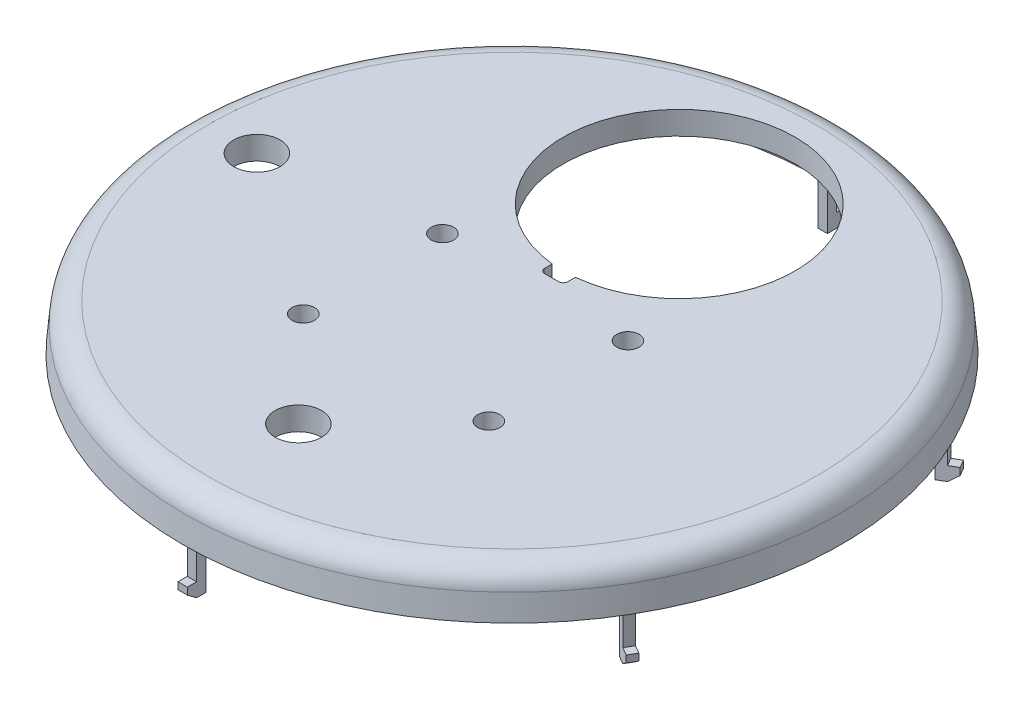
SolidWorks part; units mm, degrees
ref_plane "Front Plane" through (0, 0, 0) normal (0, 0, 1) x (1, 0, 0)
ref_plane "Top Plane" through (0, 0, 0) normal (0, 1, 0) x (1, 0, 0)
ref_plane "Right Plane" through (0, 0, 0) normal (1, 0, 0) x (0, 0, -1)
sketch "Sketch1" plane through (0, 0, 0) normal (0, 1, 0) x (1, 0, 0)
  circle A0 centre (0, 0) radius 71.05
  dimension "D1" = 142.1
extrude "Boss-Extrude1" add sketch "Sketch1" along normal blind 10 draft 5
shell "Shell4" thickness 5
sketch "Sketch2" plane through (0, 10, 0) normal (0, 1, 0) x (1, 0, 0)
  circle A0 centre (0, -46.05) radius 5
  circle A1 centre (0, 36.05) radius 25
  circle A2 centre (20, 5) radius 2.413
  circle A3 centre (20, -25) radius 2.413
  circle A4 centre (-20, -25) radius 2.413
  circle A5 centre (-20, 5) radius 2.413
  dimension "D1" = 10
  dimension "D3" = 50
  dimension "D5" = 4.826
  dimension "D6" = 4.826
  dimension "D7" = 4.826
  dimension "D8" = 4.826
  dimension "D2" = 46.05
  dimension "D4" = 36.05
  dimension "D9" = 5
  dimension "D10" = 25
  dimension "D11" = 20
  dimension "D12" = 20
  dimension "D13" = 5
extrude "Cut-Extrude1" cut sketch "Sketch2" against normal through all
sketch "Sketch3" plane through (0, 10, 0) normal (0, 1, 0) x (1, 0, 0)
  line L0 (0, 0) -> (0, 17.3356) construction
  line L1 (0, 17.3356) -> (0, 0) construction
  line L2 (0, 0) -> (-9.5982, 0) construction
  circle A0 centre (37.5, 42) radius 2.413
  circle A1 centre (-37.5, 42) radius 2.413
  circle A2 centre (37.5, -42) radius 2.413
  circle A3 centre (-37.5, -42) radius 2.413
  dimension "D3" = 4.826
  dimension "D1" = 37.5
  dimension "D2" = 42
extrude "Cut-Extrude2" [suppressed] cut sketch "Sketch3" against normal through all and the other way through all
sketch "Sketch4" [suppressed] plane through (0, 5, 0) normal (0, -1, 0) x (-1, 0, 0)
  circle A0 centre (37.5, -42) radius 4.826
  circle A1 centre (-37.5, -42) radius 4.826
  circle A2 centre (-37.5, 42) radius 4.826
  circle A3 centre (37.5, 42) radius 4.826
  dimension "D1" = 9.652
  dimension "D2" = 9.652
  dimension "D3" = 9.652
  dimension "D4" = 9.652
extrude "Boss-Extrude2" [suppressed] add sketch "Sketch4" along normal blind 5
sketch "Sketch5" [suppressed] plane through (0, 0, 0) normal (0, -1, 0) x (-1, 0, 0)
  circle A0 centre (37.5, -42) radius 2.413
  circle A1 centre (-37.5, -42) radius 2.413
  circle A2 centre (-37.5, 42) radius 2.413
  circle A3 centre (37.5, 42) radius 2.413
  dimension "D1" = 4.826
  dimension "D2" = 4.826
  dimension "D3" = 4.826
  dimension "D4" = 4.826
extrude "Cut-Extrude3" [suppressed] cut sketch "Sketch5" against normal through all
sketch "Sketch6" plane through (0, 10, 0) normal (0, 1, 0) x (1, 0, 0)
  line L0 (-25, 36.05) -> (25, 36.05) construction
  line L1 (-2.5, 14.1871) -> (2.5, 14.1871)
  line L2 (-2.5, 14.1871) -> (-2.5, 9.55)
  line L3 (-1.5, 8.55) -> (1.5, 8.55)
  line L4 (2.5, 14.1871) -> (2.5, 9.55)
  line L5 (0, 36.05) -> (0, 43.4762) construction
  circle A0 centre (0, 36.05) radius 25 construction
  arc A1 (1.5, 8.55) -> (2.5, 9.55) centre (1.5, 9.55) ccw
  arc A2 (-2.5, 9.55) -> (-1.5, 8.55) centre (-1.5, 9.55) ccw
  point P16 (0, 39.7631)
  dimension "D3" = 1
  dimension "D1" = 27.5
  dimension "D2" = 5
  dimension "D4" = 2.5
extrude "Cut-Extrude4" cut sketch "Sketch6" against normal blind 10
sketch "Sketch7" plane through (0, 10, 0) normal (0, 1, 0) x (1, 0, 0)
  line L0 (0, 36.05) -> (0, 46.1727) construction
  line L1 (0, 46.1727) -> (-8.9236, 36.05) construction
  line L2 (-8.9236, 36.05) -> (0, 36.05) construction
  circle A0 centre (-33, 30.05) radius 2.413
  circle A1 centre (33, 30.05) radius 2.413
  dimension "D1" = 4.826
  dimension "D2" = 4.826
  dimension "D3" = 6
  dimension "D4" = 6
  dimension "D5" = 33
  dimension "D6" = 33
extrude "Cut-Extrude5" [suppressed] cut sketch "Sketch7" against normal through all
fillet "Fillet1" [suppressed] radius 1
fillet "Fillet2" radius 5 1 edges at (0, 10, 70.1751)
sketch "Sketch8" [suppressed] plane through (0, 5, 0) normal (0, -1, 0) x (-1, 0, 0)
  line L0 (-37.5, -42) -> (-45.6959, -42) construction
  line L1 (-33.7739, -43.25) -> (-25.174, -43.25)
  line L2 (-33.7739, -43.25) -> (-33.7739, -40.75)
  line L3 (-33.7739, -40.75) -> (-25.174, -40.75)
  line L4 (-25.174, -43.25) -> (-25.174, -40.75)
  line L5 (-36.25, -38.3837) -> (-38.75, -38.3837)
  line L6 (-36.25, -38.3837) -> (-36.25, -29.674)
  line L7 (-36.25, -29.674) -> (-38.75, -29.674)
  line L8 (-38.75, -38.3837) -> (-38.75, -29.674)
  line L9 (-45.6959, -42) -> (-37.5, -45.4738) construction
  line L10 (-37.5, -45.4738) -> (-37.5, -42) construction
  line L11 (0, 0) -> (0, -9.0235) construction
  line L12 (36.25, -29.674) -> (38.75, -29.674)
  line L13 (38.75, -38.3837) -> (38.75, -29.674)
  line L14 (36.25, -38.3837) -> (38.75, -38.3837)
  line L15 (36.25, -38.3837) -> (36.25, -29.674)
  line L16 (33.7739, -40.75) -> (25.174, -40.75)
  line L17 (25.174, -43.25) -> (25.174, -40.75)
  line L18 (33.7739, -43.25) -> (25.174, -43.25)
  line L19 (33.7739, -43.25) -> (33.7739, -40.75)
  line L20 (0, 0) -> (-8.6355, 0) construction
  line L21 (-36.25, 29.674) -> (-38.75, 29.674)
  line L22 (-38.75, 38.3837) -> (-38.75, 29.674)
  line L23 (-36.25, 38.3837) -> (-38.75, 38.3837)
  line L24 (-36.25, 38.3837) -> (-36.25, 29.674)
  line L25 (-33.7739, 40.75) -> (-25.174, 40.75)
  line L26 (-25.174, 43.25) -> (-25.174, 40.75)
  line L27 (-33.7739, 43.25) -> (-25.174, 43.25)
  line L28 (-33.7739, 43.25) -> (-33.7739, 40.75)
  line L29 (36.25, 38.3837) -> (36.25, 29.674)
  line L30 (36.25, 38.3837) -> (38.75, 38.3837)
  line L31 (38.75, 38.3837) -> (38.75, 29.674)
  line L32 (36.25, 29.674) -> (38.75, 29.674)
  line L33 (33.7739, 43.25) -> (33.7739, 40.75)
  line L34 (33.7739, 43.25) -> (25.174, 43.25)
  line L35 (25.174, 43.25) -> (25.174, 40.75)
  line L36 (33.7739, 40.75) -> (25.174, 40.75)
  dimension "D1" = 12.326
  dimension "D2" = 12.326
  dimension "D3" = 2.5
  dimension "D4" = 2.5
  dimension "D5" = 1.25
  dimension "D6" = 1.25
extrude "Boss-Extrude3" [suppressed] add sketch "Sketch8" along normal blind 2.5
sketch "Sketch9" [suppressed] plane through (0, 0, -43.25) normal (0, 0, -1) x (-1, 0, 0)
  line L0 (-32.8387, 2.5) -> (-25.174, 5)
  line L1 (-25.174, 5) -> (-25.174, 2.5)
  line L2 (-25.174, 2.5) -> (-32.8387, 2.5)
  line L3 (32.8387, 2.5) -> (25.174, 5)
  line L4 (25.174, 5) -> (25.174, 2.5)
  line L5 (25.174, 2.5) -> (32.8387, 2.5)
extrude "Cut-Extrude6" [suppressed] cut sketch "Sketch9" against normal up to surface (86.5 mm away)
sketch "Sketch10" [suppressed] plane through (38.75, 0, 0) normal (1, 0, 0) x (0, 0, -1)
  line L0 (-37.3387, 2.5) -> (-29.674, 5)
  line L1 (-29.674, 5) -> (-29.674, 2.5)
  line L2 (-29.674, 2.5) -> (-37.3387, 2.5)
  line L3 (29.674, 5) -> (37.3387, 2.5)
  line L4 (37.3387, 2.5) -> (29.674, 2.5)
  line L5 (29.674, 2.5) -> (29.674, 5)
extrude "Cut-Extrude7" [suppressed] cut sketch "Sketch10" against normal up to surface (77.5 mm away)
sketch "Sketch11" plane through (0, 10, 0) normal (0, 1, 0) x (1, 0, 0)
  circle A0 centre (-55, 0) radius 5
  dimension "D1" = 10
  dimension "D2" = 55
extrude "Cut-Extrude8" cut sketch "Sketch11" against normal through all
sketch "Sketch12" plane through (0, 0, 0) normal (0, -1, 0) x (-1, 0, 0)
  line L0 (58.5237, 32.634) -> (60.2558, 33.634)
  line L1 (1, 67) -> (-1, 67)
  line L2 (1, 67) -> (1, 69)
  line L3 (1, 69) -> (-1, 69)
  line L4 (-1, 67) -> (-1, 69)
  line L5 (58.5237, 32.634) -> (57.5237, 34.366)
  line L6 (57.5237, 34.366) -> (59.2558, 35.366)
  line L7 (60.2558, 33.634) -> (59.2558, 35.366)
  line L8 (57.5237, -34.366) -> (59.2558, -35.366)
  line L9 (57.5237, -34.366) -> (58.5237, -32.634)
  line L10 (58.5237, -32.634) -> (60.2558, -33.634)
  line L11 (59.2558, -35.366) -> (60.2558, -33.634)
  line L12 (-1, -67) -> (-1, -69)
  line L13 (-1, -67) -> (1, -67)
  line L14 (1, -67) -> (1, -69)
  line L15 (-1, -69) -> (1, -69)
  line L16 (-58.5237, -32.634) -> (-60.2558, -33.634)
  line L17 (-58.5237, -32.634) -> (-57.5237, -34.366)
  line L18 (-57.5237, -34.366) -> (-59.2558, -35.366)
  line L19 (-60.2558, -33.634) -> (-59.2558, -35.366)
  line L20 (-57.5237, 34.366) -> (-59.2558, 35.366)
  line L21 (-57.5237, 34.366) -> (-58.5237, 32.634)
  line L22 (-58.5237, 32.634) -> (-60.2558, 33.634)
  line L23 (-59.2558, 35.366) -> (-60.2558, 33.634)
  point P28 (0, 0)
  dimension "D1" = 2
  dimension "D2" = 2
  dimension "D3" = 1
  dimension "D4" = 67
  dimension "D5" = 6
extrude "Boss-Extrude4" add sketch "Sketch12" along normal blind 7.5
sketch "Sketch13" plane through (0, -7.5, 0) normal (0, -1, 0) x (-1, 0, 0)
  line L0 (-58.5237, -32.634) -> (-61.9878, -34.634)
  line L1 (-1, -67) -> (1, -67)
  line L2 (-1, -67) -> (-1, -71)
  line L3 (-1, -71) -> (1, -71)
  line L4 (1, -67) -> (1, -71)
  line L5 (-58.5237, -32.634) -> (-57.5237, -34.366)
  line L6 (-57.5237, -34.366) -> (-60.9878, -36.366)
  line L7 (-61.9878, -34.634) -> (-60.9878, -36.366)
  line L8 (-57.5237, 34.366) -> (-60.9878, 36.366)
  line L9 (-57.5237, 34.366) -> (-58.5237, 32.634)
  line L10 (-58.5237, 32.634) -> (-61.9878, 34.634)
  line L11 (-60.9878, 36.366) -> (-61.9878, 34.634)
  line L12 (1, 67) -> (1, 71)
  line L13 (1, 67) -> (-1, 67)
  line L14 (-1, 67) -> (-1, 71)
  line L15 (1, 71) -> (-1, 71)
  line L16 (58.5237, 32.634) -> (61.9878, 34.634)
  line L17 (58.5237, 32.634) -> (57.5237, 34.366)
  line L18 (57.5237, 34.366) -> (60.9878, 36.366)
  line L19 (61.9878, 34.634) -> (60.9878, 36.366)
  line L20 (57.5237, -34.366) -> (60.9878, -36.366)
  line L21 (57.5237, -34.366) -> (58.5237, -32.634)
  line L22 (58.5237, -32.634) -> (61.9878, -34.634)
  line L23 (60.9878, -36.366) -> (61.9878, -34.634)
  point P27 (0, 0)
  dimension "D1" = 2
  dimension "D2" = 4
  dimension "D3" = 6
extrude "Boss-Extrude5" add sketch "Sketch13" along normal blind 3
sketch "Sketch14" plane through (1, 0, 0) normal (1, 0, 0) x (0, 0, -1)
  line L0 (71, -9) -> (69, -10.5)
  line L1 (71, -10.5) -> (71, -7.5) construction
  line L2 (71, -10.5) -> (67, -10.5) construction
  line L5 (69, -10.5) -> (71, -10.5)
  line L6 (71, -10.5) -> (71, -9)
  dimension "D1" = 2
extrude "Cut-Extrude9" cut sketch "Sketch14" against normal blind 3
sketch "Sketch16" plane through (0.5, 0, 0.866) normal (0.5, 0, 0.866) x (0.866, 0, -0.5)
  line L0 (71, -9) -> (69, -10.5)
  line L1 (71, -10.5) -> (71, -7.5) construction
  line L2 (71, -10.5) -> (67, -10.5) construction
  line L3 (69, -10.5) -> (71, -10.5)
  line L4 (71, -10.5) -> (71, -9)
extrude "Cut-Extrude10" cut sketch "Sketch16" against normal blind 3
sketch "Sketch17" plane through (-0.5, 0, 0.866) normal (-0.5, 0, 0.866) x (0.866, 0, 0.5)
  line L0 (71, -9) -> (69, -10.5)
  line L1 (71, -10.5) -> (71, -7.5) construction
  line L2 (71, -10.5) -> (67, -10.5) construction
  line L3 (69, -10.5) -> (71, -10.5)
  line L4 (71, -10.5) -> (71, -9)
extrude "Cut-Extrude11" cut sketch "Sketch17" against normal blind 3
sketch "Sketch18" plane through (-1, 0, 0) normal (-1, 0, 0) x (0, 0, 1)
  line L0 (71, -9) -> (69, -10.5)
  line L1 (71, -10.5) -> (71, -7.5) construction
  line L2 (71, -10.5) -> (67, -10.5) construction
  line L3 (69, -10.5) -> (71, -10.5)
  line L4 (71, -10.5) -> (71, -9)
extrude "Cut-Extrude12" cut sketch "Sketch18" against normal blind 3
sketch "Sketch19" plane through (-0.5, 0, -0.866) normal (-0.5, 0, -0.866) x (-0.866, 0, 0.5)
  line L0 (71, -9) -> (69, -10.5)
  line L1 (71, -10.5) -> (71, -7.5) construction
  line L2 (71, -10.5) -> (67, -10.5) construction
  line L3 (69, -10.5) -> (71, -10.5)
  line L4 (71, -10.5) -> (71, -9)
extrude "Cut-Extrude13" cut sketch "Sketch19" against normal blind 3
sketch "Sketch20" plane through (0.5, 0, -0.866) normal (0.5, 0, -0.866) x (-0.866, 0, -0.5)
  line L0 (71, -9) -> (69, -10.5)
  line L1 (71, -10.5) -> (71, -7.5) construction
  line L2 (71, -10.5) -> (67, -10.5) construction
  line L3 (69, -10.5) -> (71, -10.5)
  line L4 (71, -10.5) -> (71, -9)
extrude "Cut-Extrude14" cut sketch "Sketch20" against normal blind 3
